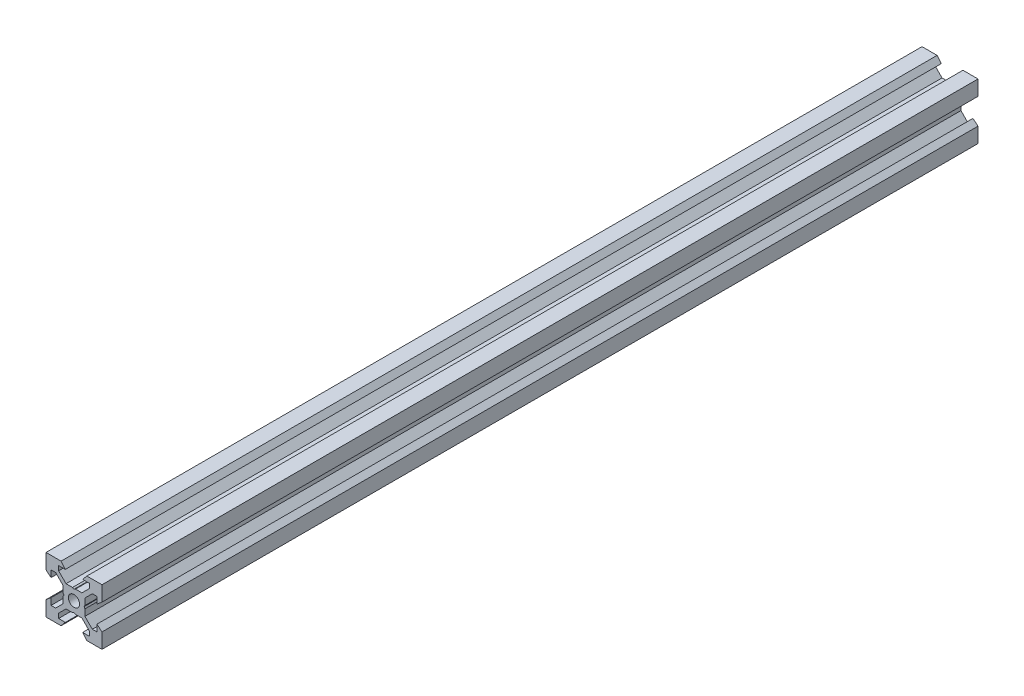
SolidWorks part; units mm, degrees
ref_plane "Front Plane" through (0, 0, 0) normal (0, 0, 1) x (1, 0, 0)
ref_plane "Top Plane" through (0, 0, 0) normal (0, 1, 0) x (1, 0, 0)
ref_plane "Right Plane" through (0, 0, 0) normal (1, 0, 0) x (0, 0, -1)
sketch "Sketch1" plane through (0, 0, 0) normal (0, 0, 1) x (1, 0, 0)
  line L0 (10, 10) -> (4.6104, 10) construction
  line L1 (10, 10) -> (10, 4.6104) construction
  line L2 (10, -10) -> (10, -4.6104) construction
  line L3 (10, -10) -> (4.6104, -10) construction
  line L4 (10, 10) -> (10, 4.6104)
  line L5 (6.5607, 5.5) -> (8.2, 5.5)
  line L6 (5.5, 8.2) -> (5.5, 6.5607)
  line L7 (10, 10) -> (4.6104, 10)
  line L8 (10, 10) -> (10, 4.6104)
  line L9 (6.5607, 5.5) -> (3.9, 2.8393)
  line L10 (5.5, 6.5607) -> (2.8393, 3.9)
  line L11 (10, 4.6104) -> (8.2, 3.1)
  line L12 (4.6104, 10) -> (3.1, 8.2)
  line L13 (8.2, 3.1) -> (8.2, 5.5)
  line L14 (3.1, 8.2) -> (5.5, 8.2)
  line L15 (-6.5607, 5.5) -> (-8.2, 5.5)
  line L16 (6.5607, -5.5) -> (8.2, -5.5)
  line L17 (3.1, -8.2) -> (5.5, -8.2)
  line L18 (8.2, -3.1) -> (8.2, -5.5)
  line L19 (4.6104, -10) -> (3.1, -8.2)
  line L20 (10, -4.6104) -> (8.2, -3.1)
  line L21 (0.5196, -3.9) -> (0, -3.6)
  line L22 (0.5196, 3.9) -> (0, 3.6)
  line L23 (3.6, 0) -> (3.9, -0.5196)
  line L24 (3.9, 0.5196) -> (3.6, 0)
  line L25 (3.9, 0.5196) -> (3.9, 2.8393)
  line L26 (2.8393, 3.9) -> (0.5196, 3.9)
  line L27 (3.9, -2.8393) -> (3.9, -0.5196)
  line L28 (2.8393, -3.9) -> (0.5196, -3.9)
  line L29 (5.5, -6.5607) -> (2.8393, -3.9)
  line L30 (6.5607, -5.5) -> (3.9, -2.8393)
  line L31 (10, -10) -> (10, -4.6104)
  line L32 (10, -10) -> (4.6104, -10)
  line L33 (5.5, -8.2) -> (5.5, -6.5607)
  line L34 (-6.5607, -5.5) -> (-8.2, -5.5)
  line L35 (10, -10) -> (10, -4.6104)
  line L36 (0, 0) -> (0, 8.2) construction
  line L37 (-10, -10) -> (-4.6104, -10) construction
  line L38 (-10, -10) -> (-10, -4.6104) construction
  line L39 (-10, 10) -> (-10, 4.6104) construction
  line L40 (-10, 10) -> (-4.6104, 10) construction
  line L41 (-10, -10) -> (-10, -4.6104)
  line L43 (-5.5, -8.2) -> (-5.5, -6.5607)
  line L44 (-10, -10) -> (-4.6104, -10)
  line L45 (-10, -10) -> (-10, -4.6104)
  line L46 (-6.5607, -5.5) -> (-3.9, -2.8393)
  line L47 (-5.5, -6.5607) -> (-2.8393, -3.9)
  line L48 (-2.8393, -3.9) -> (-0.5196, -3.9)
  line L49 (-3.9, -2.8393) -> (-3.9, -0.5196)
  line L50 (-2.8393, 3.9) -> (-0.5196, 3.9)
  line L51 (-3.9, 0.5196) -> (-3.9, 2.8393)
  line L52 (-3.9, 0.5196) -> (-3.6, 0)
  line L53 (-3.6, 0) -> (-3.9, -0.5196)
  line L54 (-0.5196, 3.9) -> (0, 3.6)
  line L55 (-0.5196, -3.9) -> (0, -3.6)
  line L56 (-10, -4.6104) -> (-8.2, -3.1)
  line L57 (-4.6104, -10) -> (-3.1, -8.2)
  line L58 (-8.2, -3.1) -> (-8.2, -5.5)
  line L59 (-3.1, -8.2) -> (-5.5, -8.2)
  line L60 (-10, -10) -> (10, -10) construction
  line L61 (-10, -10) -> (-10, 10) construction
  line L62 (-3.1, 8.2) -> (-5.5, 8.2)
  line L63 (-8.2, 3.1) -> (-8.2, 5.5)
  line L64 (-4.6104, 10) -> (-3.1, 8.2)
  line L65 (-10, 4.6104) -> (-8.2, 3.1)
  line L66 (-5.5, 6.5607) -> (-2.8393, 3.9)
  line L67 (-6.5607, 5.5) -> (-3.9, 2.8393)
  line L68 (-10, 10) -> (-10, 4.6104)
  line L69 (-10, 10) -> (-4.6104, 10)
  line L70 (-5.5, 8.2) -> (-5.5, 6.5607)
  line L71 (-10, 10) -> (10, 10) construction
  line L72 (-10, 10) -> (-10, 4.6104)
  line L73 (10, -10) -> (10, 10) construction
  line L74 (-10, -10) -> (10, 10) construction
  line L75 (-10, 10) -> (10, -10) construction
  circle A0 centre (0, 0) radius 2
  dimension "D7" = 4
  dimension "D1" = 20
  dimension "D2" = 5.3896
  dimension "D3" = 4.5
  dimension "D4" = 50
  dimension "D5" = 1.8
  dimension "D6" = 1.5104
  dimension "D8" = 5.5
  dimension "D9" = 120
  dimension "D10" = 0.3
  dimension "D11" = 2.3197
  dimension "D12" = 7.8
  dimension "D13" = 7.8
  dimension "D14" = 1.5
  dimension "D15" = 2.6607
extrude "Boss-Extrude1" add sketch "Sketch1" along normal mid plane 313.05 contours L70 L62 L64 L69 L68 L65 L63 L15 L67 L51 L52 L53 L49 L46 L34 L58 L56 L41 L44 L57 L59 L43 L47 L48 L55 L21 L28 L29 L33 L17 L19 L32 L31 L20 L18 L16 L30 L27 L23 L24 L25 L9 L5 L13 L11 L4 L7 L12 L14 L6 L10
